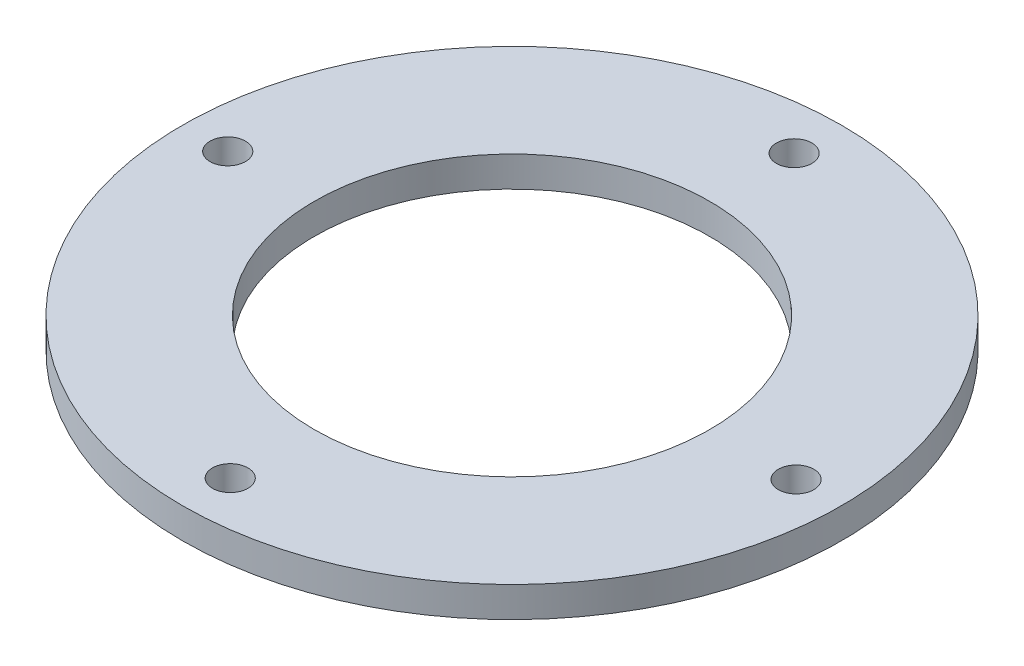
SolidWorks part; units mm, degrees
ref_plane "Front Plane" through (0, 0, 0) normal (0, 0, 1) x (1, 0, 0)
ref_plane "Top Plane" through (0, 0, 0) normal (0, 1, 0) x (1, 0, 0)
ref_plane "Right Plane" through (0, 0, 0) normal (1, 0, 0) x (0, 0, -1)
sketch "Sketch1" plane through (0, 0, 0) normal (0, 1, 0) x (1, 0, 0)
  circle A0 centre (0, 0) radius 32.5
  circle A1 centre (0, 0) radius 19.5
  dimension "D1" = 65
  dimension "D2" = 39
extrude "Boss-Extrude2" add sketch "Sketch1" along normal blind 3
sketch "Sketch2" plane through (0, 3, 0) normal (0, 1, 0) x (1, 0, 0)
  circle A0 centre (0, -27.7889) radius 1.75
  dimension "D1" = 3.5
extrude "Cut-Extrude2" cut sketch "Sketch2" against normal through all both and the other way through all
sketch "Sketch5" plane through (0, 3, 0) normal (0, 1, 0) x (1, 0, 0)
  line L0 (0, 32.5) -> (0, 29.79)
  circle A0 centre (0.0578, 27.7663) radius 1.75
  circle A1 centre (0, 0) radius 32.5 construction
  dimension "D1" = 3.5
  dimension "D2" = 2.71
extrude "Cut-Extrude4" cut sketch "Sketch5" against normal through all both and the other way through all contours A0
sketch "Sketch13" plane through (0, 3, 0) normal (0, 1, 0) x (1, 0, 0)
  line L0 (-32.5, 0) -> (-29.79, 0)
  line L1 (32.5, 0) -> (29.79, 0)
  circle A0 centre (0, 0) radius 32.5 construction
  circle A1 centre (-28.0274, -0.004) radius 1.75
  circle A2 centre (28.0162, 0) radius 1.75
  dimension "D3" = 3.5
  dimension "D4" = 3.5
  dimension "D1" = 2.71
  dimension "D2" = 2.71
extrude "Cut-Extrude12" cut sketch "Sketch13" against normal through all both and the other way through all contours A1 | A2
